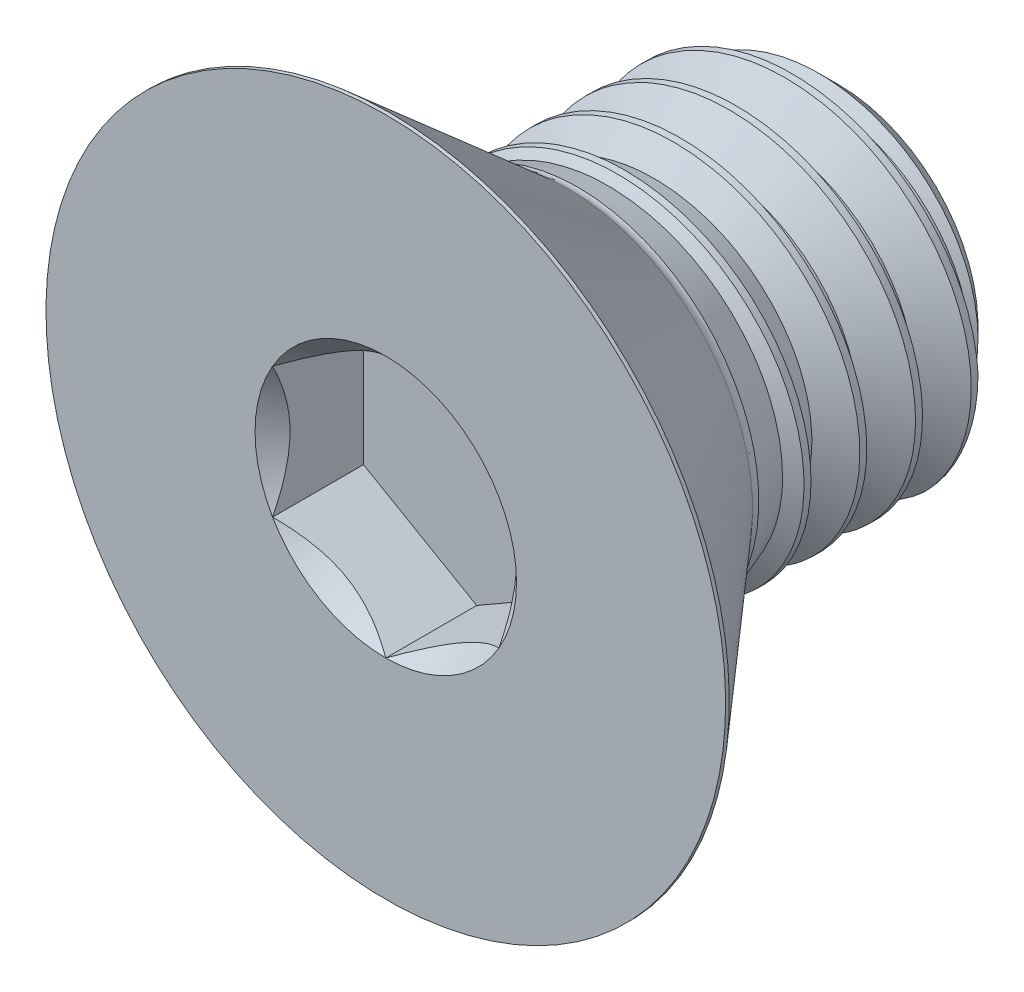
SolidWorks part; units mm, degrees
ref_plane "Front Plane" through (0, 0, 0) normal (0, 0, 1) x (1, 0, 0)
ref_plane "Top Plane" through (0, 0, 0) normal (0, 1, 0) x (1, 0, 0)
ref_plane "Right Plane" through (0, 0, 0) normal (1, 0, 0) x (0, 0, -1)
sketch "Sketch1" plane through (0, 0, 0) normal (1, 0, 0) x (0, 0, -1)
  line L0 (-7.9375, 0) -> (7.9375, 0) construction
  line L1 (-7.9375, 0) -> (-7.9375, 11.9126)
  line L2 (-7.9375, 11.9126) -> (-7.81, 11.9126)
  line L3 (-7.81, 11.9126) -> (-1.5621, 6.4814)
  line L4 (-7.81, -11.9126) -> (-1.5621, -6.4814)
  line L5 (7.9375, 0) -> (7.9375, 6.35)
  line L6 (7.9375, 6.35) -> (-1.5621, 6.35)
  line L7 (6.4721, 6.35) -> (7.9375, 4.8846)
  line L8 (7.8154, 6.5615) -> (8.7923, 4.8694) construction
  line L9 (8.7923, 4.8694) -> (9.7692, 6.5615) construction
  line L10 (9.7692, 6.5615) -> (7.8154, 6.5615) construction
  line L11 (7.8764, 6.4558) -> (9.7082, 6.4558)
  line L12 (9.7082, 6.4558) -> (8.9144, 5.0809)
  line L13 (8.9144, 5.0809) -> (8.6702, 5.0809)
  line L14 (8.6702, 5.0809) -> (7.8764, 6.4558)
  line L15 (8.7923, 5.0809) -> (8.7923, 4.8694) construction
  line L16 (7.9375, 6.35) -> (9.6471, 6.35) construction
  line L17 (8.7923, 6.5615) -> (8.7923, 6.35) construction
  line L18 (7.9375, -6.35) -> (-1.5621, -6.35)
  arc A0 (-1.5621, 6.4814) -> (-1.2107, 6.35) centre (-1.2107, 6.8857) ccw
  point P2 (0, 0)
  point P23 (-4.7498, 0)
  point P27 (8.7923, 6.4558)
  point P30 (5.0067, -6.35)
  point P31 (-1.5621, 11.9126)
  point P34 (-7.81, -11.9126)
  dimension "Length" = 15.875
  dimension "Head Height" = 6.3754
  dimension "Head Diameter" = 23.8252
  dimension "Countersink Angle" = 82
  dimension "Screw Size Decimal Equivalent" = 12.7
  dimension "Pitch" = 1.9538
  dimension "D4" = 0.2442
  dimension "D3" = 45
  dimension "D5" = 1.4654
  dimension "D6" = 3.1877
  dimension "D1" = 2.9308
  dimension "D7" = 0.1275
sketch "Sketch8" plane through (0, 0, 0) normal (0, 0, 1) x (1, 0, 0)
  line L1 (0, 4.5827) -> (-3.9688, 2.2914)
  line L2 (-3.9688, 2.2914) -> (-3.9688, -2.2914)
  line L3 (-3.9688, -2.2914) -> (0, -4.5827)
  line L4 (0, -4.5827) -> (3.9688, -2.2914)
  line L5 (3.9688, -2.2914) -> (3.9688, 2.2914)
  line L6 (3.9688, 2.2914) -> (0, 4.5827)
  circle A0 centre (0, 0) radius 3.9688 construction
  dimension "Drive Size" = 7.9375
sketch "Sketch2" plane through (0, 0, 0) normal (1, 0, 0) x (0, 0, -1)
  line L0 (-7.81, 11.9126) -> (-1.5621, 6.4814) construction
  line L1 (-7.9375, 0) -> (-7.9375, 11.9126) construction
  line L2 (-7.81, 11.9126) -> (-1.5621, 6.4814)
  line L3 (-7.9375, 0) -> (-7.9375, 11.9126)
  line L4 (-7.9375, 11.9126) -> (-7.81, 11.9126) construction
  line L5 (-7.9375, 11.9126) -> (-7.81, 11.9126)
  line L6 (-1.2107, 6.35) -> (6.4721, 6.35)
  line L7 (6.4721, 6.35) -> (7.9375, 4.8846)
  line L8 (7.9375, 4.8846) -> (7.9375, 0)
  line L9 (7.9375, 0) -> (-7.9375, 0)
  arc A0 (-1.5621, 6.4814) -> (-1.2107, 6.35) centre (-1.2107, 6.8857) ccw construction
  arc A1 (-1.5621, 6.4814) -> (-1.2107, 6.35) centre (-1.2107, 6.8857) ccw
revolve "Revolve1" add sketch "Sketch2" angle 360 about L9
sketch "Sketch9" plane through (0, 0, 7.9375) normal (0, 0, 1) x (1, 0, 0)
  line L0 (3.9688, -2.2914) -> (3.9688, 2.2914) construction
  line L1 (0, -4.5827) -> (3.9688, -2.2914) construction
  line L2 (-3.9688, -2.2914) -> (0, -4.5827) construction
  line L3 (-3.9688, 2.2914) -> (-3.9688, -2.2914) construction
  line L4 (0, 4.5827) -> (-3.9688, 2.2914) construction
  line L5 (3.9688, 2.2914) -> (0, 4.5827) construction
  line L6 (3.9688, -2.2914) -> (3.9688, 2.2914)
  line L7 (0, -4.5827) -> (3.9688, -2.2914)
  line L8 (-3.9688, -2.2914) -> (0, -4.5827)
  line L9 (-3.9688, 2.2914) -> (-3.9688, -2.2914)
  line L10 (0, 4.5827) -> (-3.9688, 2.2914)
  line L11 (3.9688, 2.2914) -> (0, 4.5827)
sketch "Sketch10" plane through (0, 0, 7.9375) normal (0, 0, 1) x (1, 0, 0)
  circle A0 centre (0, 0) radius 4.5827
extrude "Cut-Extrude2" cut sketch "Sketch10" against normal up to vertex (3.1877 mm away) draft 45 up to point (0, 0, 4.7498)
extrude "Cut-Extrude1" cut sketch "Sketch9" against normal up to vertex (3.1877 mm away) up to point (0, 0, 4.7498)
ref_plane "Plane1" through (0, 0, 1.2107) normal (0, 0, 1) x (1, 0, 0)
split "Split1" trim tools "Plane1" bodies to split 111 resulting bodies 105 106
sketch "Sketch3" plane through (0, 0, -7.9375) normal (0, 0, -1) x (-1, 0, 0)
  circle A0 centre (0, 0) radius 6.35 construction
  circle A1 centre (0, 0) radius 6.35
curve "Helix/Spiral1" pitch 1.9538 height 15.875 turns 8.125
sketch "Sketch4" plane through (0, 0, 0) normal (1, 0, 0) x (0, 0, -1)
  line L0 (7.8764, 6.4558) -> (9.7082, 6.4558) construction
  line L1 (8.6702, 5.0809) -> (7.8764, 6.4558) construction
  line L2 (8.9144, 5.0809) -> (8.6702, 5.0809) construction
  line L3 (9.7082, 6.4558) -> (8.9144, 5.0809) construction
  line L4 (7.8764, 6.4558) -> (9.7082, 6.4558)
  line L5 (8.6702, 5.0809) -> (7.8764, 6.4558)
  line L6 (8.9144, 5.0809) -> (8.6702, 5.0809)
  line L7 (9.7082, 6.4558) -> (8.9144, 5.0809)
sweep "Cut-Sweep1" cut profiles "Sketch4" path "Helix/Spiral1"
sketch "Sketch7" plane through (0, 0, 1.2107) normal (0, 0, 1) x (1, 0, 0)
  circle A0 centre (0, 0) radius 6.35
extrude "Boss-Extrude2" add sketch "Sketch7" against normal up to next (9.1482 mm away) draft 20
equation "\"D4@Sketch1\" = \"Pitch@Sketch1\" / 8"
equation "\"D5@Sketch1\"=\"Pitch@Sketch1\"*0.75"
equation "\"D4@Helix/Spiral1\"=\"Pitch@Sketch1\""
equation "\"D3@Helix/Spiral1\"=\"Length@Sketch1\""
equation "\"D6@Sketch1\"=\"Head Height@Sketch1\"/2"
equation "\"D1@Sketch1\"=\"Pitch@Sketch1\"*1.5"
equation "\"D7@Sketch1\"=\"Head Height@Sketch1\"*0.02"
